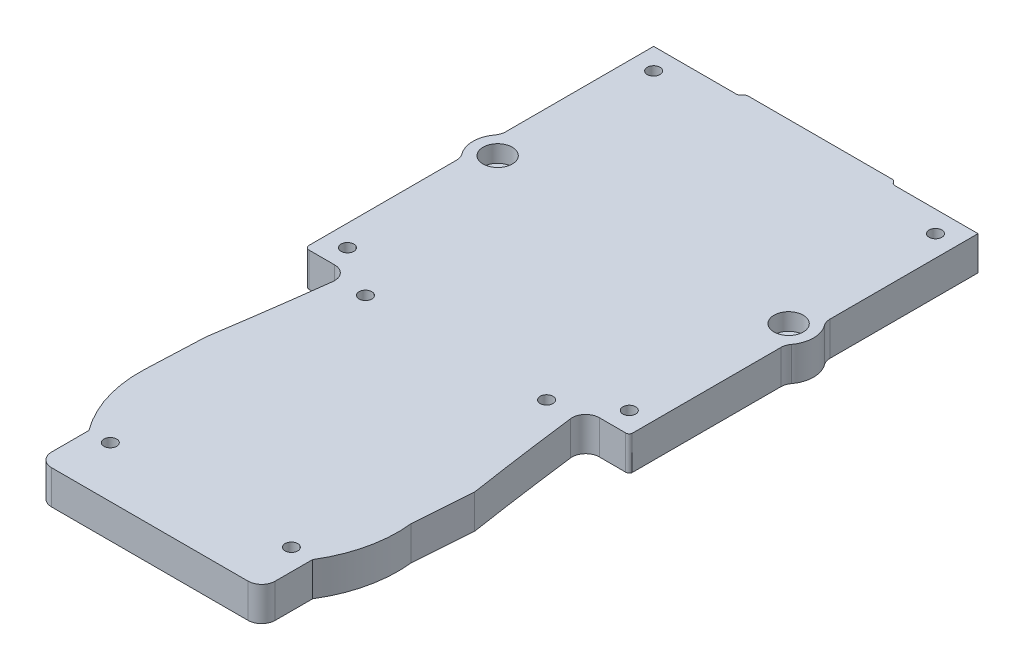
SolidWorks part; units mm, degrees
ref_plane "Front Plane" through (0, 0, 0) normal (0, 0, 1) x (1, 0, 0)
ref_plane "Top Plane" through (0, 0, 0) normal (0, 1, 0) x (1, 0, 0)
ref_plane "Right Plane" through (0, 0, 0) normal (1, 0, 0) x (0, 0, -1)
sketch "Sketch1" plane through (0, 0, 0) normal (0, 1, 0) x (1, 0, 0)
  line L20 (6.1173, 0) -> (6.1173, -6.985)
  line L26 (52.5617, 49.6761) -> (56.5298, 49.6761)
  line L28 (2.2915, 49.6761) -> (-2.471, 49.6761)
  line L31 (-3.2647, 50.4698) -> (-3.2647, 77.9626)
  line L34 (8.6573, -9.525) -> (45.3177, -9.525)
  line L36 (47.8577, -6.985) -> (47.8577, 0)
  line L37 (13.5723, 115.5573) -> (40.4027, 115.5573)
  line L40 (2.2915, 49.6761) -> (1.4133, 49.6761)
  line L42 (51.6835, 49.6761) -> (52.5617, 49.6761)
  line L45 (41.7776, 114.7636) -> (57.2716, 114.7636)
  line L47 (1.4446, 14.9527) -> (1.9181, 26.0378)
  line L48 (-3.2647, 114.7636) -> (12.1974, 114.7636)
  line L49 (51.2547, 14.9527) -> (52.0569, 26.0378)
  line L50 (57.2716, 114.7636) -> (57.2716, 87.1374)
  line L57 (-3.2647, 87.1374) -> (-3.2647, 114.7636)
  line L58 (57.2716, 77.9626) -> (57.2716, 50.1872)
  arc A14 (51.6835, 49.6761) -> (49.1629, 46.8225) centre (51.6835, 47.1361) ccw
  arc A21 (6.1173, 0) -> (1.4446, 14.9527) centre (24.8876, 14.0721) cw
  arc A22 (47.8577, 0) -> (51.2547, 14.9527) centre (27.9359, 12.3882) ccw
  arc A23 (1.9181, 26.0378) -> (4.8121, 46.8225) centre (-709.2046, 135.6465) ccw
  arc A25 (52.0569, 26.0378) -> (49.1629, 46.8225) centre (763.1796, 135.6465) cw
  arc A27 (47.8577, -6.985) -> (45.3177, -9.525) centre (45.3177, -6.985) cw
  arc A28 (8.6573, -9.525) -> (6.1173, -6.985) centre (8.6573, -6.985) cw
  arc A29 (2.2915, 49.6761) -> (4.8121, 46.8225) centre (2.2915, 47.1361) cw
  arc A31 (41.0902, 115.1605) -> (40.4027, 115.5573) centre (40.4027, 114.7636) ccw
  arc A32 (12.8848, 115.1605) -> (13.5723, 115.5573) centre (13.5723, 114.7636) cw
  arc A33 (41.0902, 115.1605) -> (41.7776, 114.7636) centre (41.7776, 115.5573) ccw
  arc A34 (12.8848, 115.1605) -> (12.1974, 114.7636) centre (12.1974, 115.5573) cw
  arc A36 (-3.2647, 50.4698) -> (-2.471, 49.6761) centre (-2.471, 50.4698) ccw
  arc A37 (56.5298, 49.6761) -> (57.2716, 50.1872) centre (56.6452, 50.3025) ccw
  circle A38 centre (-0.1669, 82.55) radius 1.1906
  circle A39 centre (54.1419, 82.55) radius 1.1906
  arc A40 (-3.7635, 79.4742) -> (-3.7635, 85.6258) centre (0.3897, 82.55) cw
  arc A41 (-3.7635, 79.4742) -> (-3.2647, 77.9626) centre (-5.8047, 77.9626) cw
  arc A42 (-3.2647, 87.1374) -> (-3.7635, 85.6258) centre (-5.8047, 87.1374) cw
  arc A43 (57.7704, 85.6258) -> (57.7704, 79.4742) centre (53.6171, 82.55) cw
  arc A44 (57.7704, 79.4742) -> (57.2716, 77.9626) centre (59.8116, 77.9626) ccw
  arc A45 (57.2716, 87.1374) -> (57.7704, 85.6258) centre (59.8116, 87.1374) ccw
  dimension "D3" = 60.5363
  dimension "D4" = 15.494
  dimension "D5" = 49.392
  dimension "D6" = 2.54
  dimension "D13" = 0.7937
  dimension "D14" = 0.7938
  dimension "D15" = 2.54
  dimension "D16" = 64.5764
  dimension "D9" = 0.6369
  dimension "D19" = 2.54
  dimension "D20" = 2.54
  dimension "D10" = 15.4622
  dimension "D11" = 26.8305
  dimension "D12" = 44.3508
extrude "Boss-Extrude1" add sketch "Sketch1" along normal blind 6.35 contours A45 L50 L45 A33 A31 L37 A32 A34 L48 L57 A42 A40 A41 L31 A36 L28 A29 A23 L47 A21 L20 A28 L34 A27 L36 A22 L49 A25 A14 L42 L26 A37 L58 A44 A43 A39 A38
sketch "Sketch2" plane through (0, 6.35, 0) normal (0, 1, 0) x (1, 0, 0)
  circle A0 centre (10.0861, 0) radius 1.1906
  circle A1 centre (43.8889, 0) radius 1.1906
  circle A2 centre (10.0861, 47.625) radius 1.1906
  circle A3 centre (43.8889, 47.625) radius 1.1906
  circle A123 centre (0.704, 53.6448) radius 1.1906
  circle A124 centre (0.704, 110.7948) radius 1.1906
  circle A125 centre (53.3028, 53.6448) radius 1.1906
  circle A126 centre (53.3028, 110.7948) radius 1.1906
extrude "Cut-Extrude1" cut sketch "Sketch2" against normal blind 5.9531
sketch "Sketch3" plane through (0, 6.35, 0) normal (0, 1, 0) x (1, 0, 0)
  circle A0 centre (-0.1669, 82.55) radius 2.7285
  circle A1 centre (54.1419, 82.55) radius 2.7285
extrude "Cut-Extrude2" cut sketch "Sketch3" against normal blind 3.175
